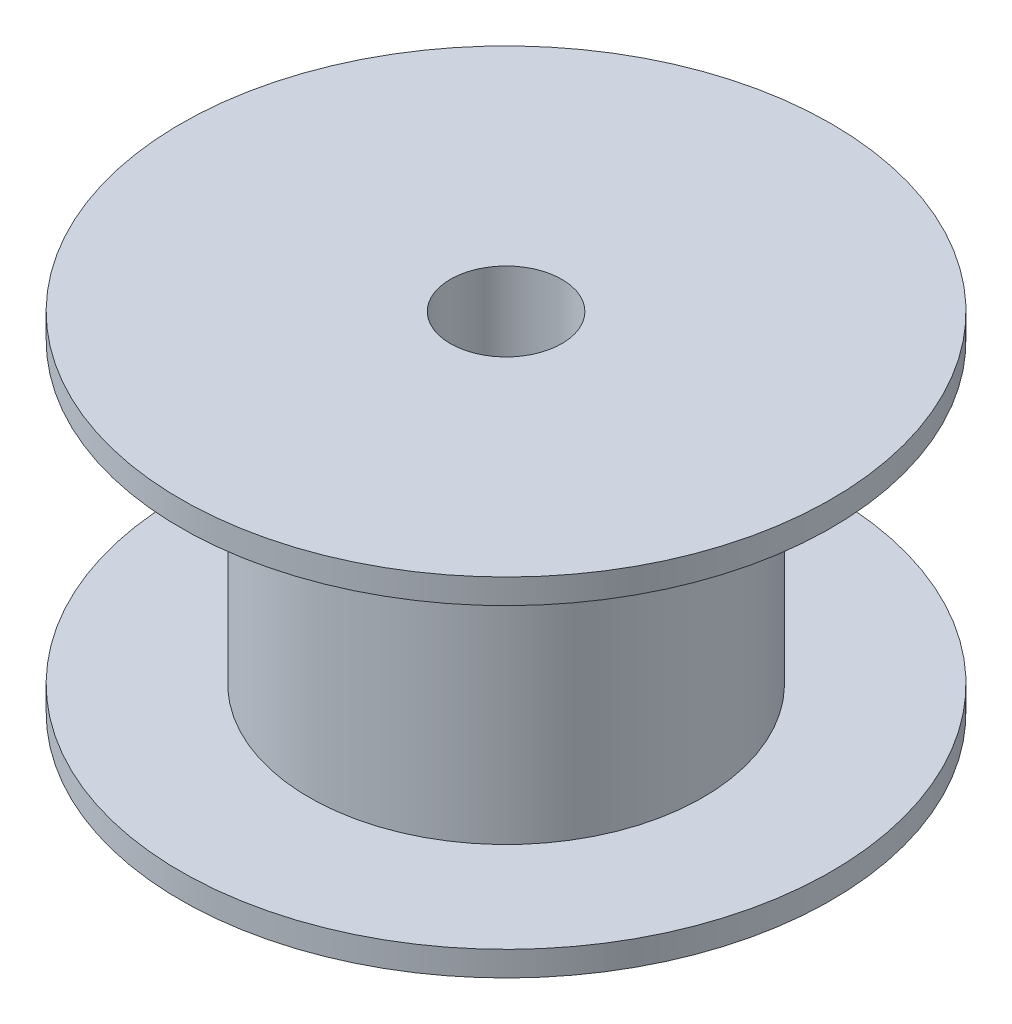
SolidWorks part; units mm, degrees
ref_plane "Front Plane" through (0, 0, 0) normal (0, 0, 1) x (1, 0, 0)
ref_plane "Top Plane" through (0, 0, 0) normal (0, 1, 0) x (1, 0, 0)
ref_plane "Right Plane" through (0, 0, 0) normal (1, 0, 0) x (0, 0, -1)
sketch "Sketch1" plane through (0, 0, 0) normal (1, 0, 0) x (0, 0, -1)
  line L0 (0, -7) -> (0, 7)
  line L1 (0, 7) -> (-13.1125, 7)
  line L2 (-13.1125, 7) -> (-13.1125, 6)
  line L3 (-13.1125, 6) -> (-7.9375, 6)
  line L4 (-7.9375, 6) -> (-7.9375, -6)
  line L5 (-7.9375, -6) -> (-13.1125, -6)
  line L6 (-13.1125, -6) -> (-13.1125, -7)
  line L7 (-13.1125, -7) -> (0, -7)
  point P14 (0, 0)
  dimension "D1" = 1
  dimension "D2" = 12
  dimension "D3" = 7.9375
  dimension "D4" = 5.175
revolve "Revolve1" add sketch "Sketch1" angle 360 about L0
hole_wizard "#8 Clearance Hole1" positions "Sketch3" profile "Sketch2" hole size "#8" standard "ANSI Inch" end condition through all
sketch "Sketch3" plane through (0, 7, 0) normal (0, 1, 0) x (1, 0, 0)
  point P0 (0, 0)
sketch "Sketch2" plane through (0, 7, 0) normal (1, 0, 0) x (0, 0, 1)
  line L0 (0, 0) -> (0, 14)
  line L1 (0, 14) -> (2.2479, 14)
  line L2 (2.2479, 14) -> (2.2479, 0)
  line L5 (2.2479, 0) -> (0, 0)
  line L11 (0, -6.35) -> (0, 107.95) construction
  dimension "Thru Hole Dia." = 4.4958
  dimension "Thru Hole Depth" = 14
